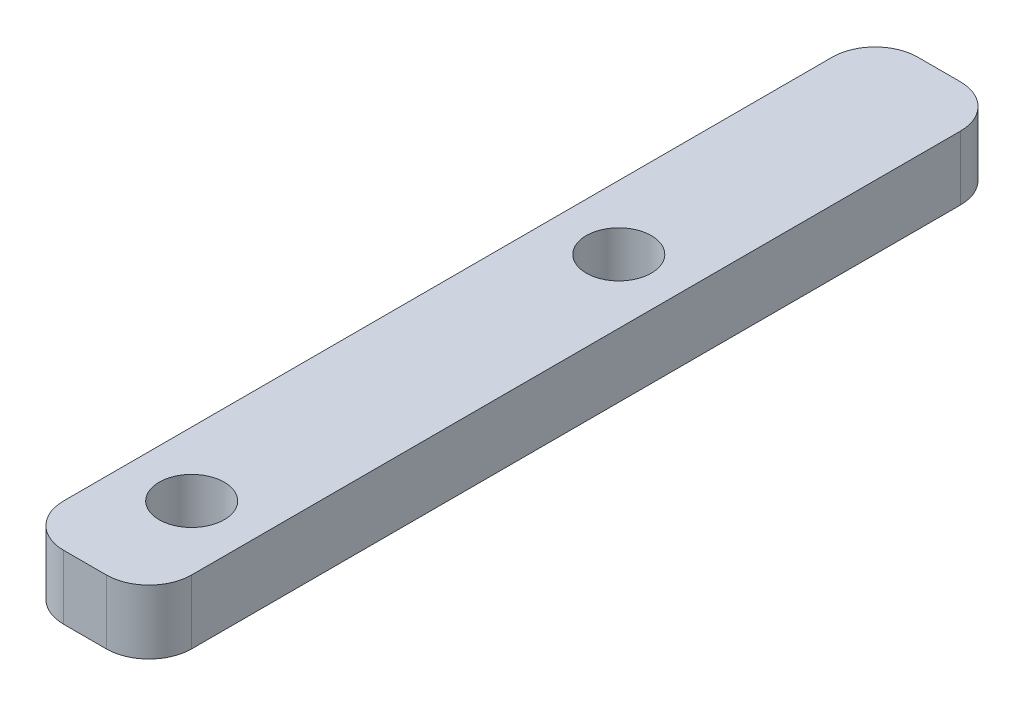
SolidWorks part; units mm, degrees
material "Thornel Mat VMA"
ref_plane "前视基准面" through (0, 0, 0) normal (0, 0, 1) x (1, 0, 0)
ref_plane "上视基准面" through (0, 0, 0) normal (0, 1, 0) x (1, 0, 0)
ref_plane "右视基准面" through (0, 0, 0) normal (1, 0, 0) x (0, 0, -1)
other "Configuration Table"
sketch "草图1" plane through (0, 0, 0) normal (0, 1, 0) x (1, 0, 0)
  line L1 (-3, -20) -> (3, -20)
  line L2 (-3, -20) -> (-3, 20)
  line L3 (-3, 20) -> (3, 20)
  line L4 (3, -20) -> (3, 20)
  line L5 (-3, -20) -> (3, 20) construction
  line L6 (-3, 20) -> (3, -20) construction
  point P0 (0, 0)
  dimension "D1" = 6
  dimension "D2" = 40
extrude "凸台-拉伸1" add sketch "草图1" along normal blind 3
fillet "圆角1" radius 2 4 edges at (-3, 1.5, 20) (-3, 1.5, -20) (3, 1.5, -20) (3, 1.5, 20)
sketch "草图2" plane through (0, 3, 0) normal (0, 1, 0) x (1, 0, 0)
  line L0 (-1, -20) -> (1, -20) construction
  circle A0 centre (0, 5) radius 1.525
  circle A1 centre (0, -15) radius 1.525
  point P4 (0, 0)
  point P8 (0, -15)
  point P9 (0, 0)
  dimension "D1" = 20
  dimension "D2" = 3.05
  dimension "D3" = 3.05
  dimension "D4" = 5
extrude "切除-拉伸1" cut sketch "草图2" against normal blind 3
